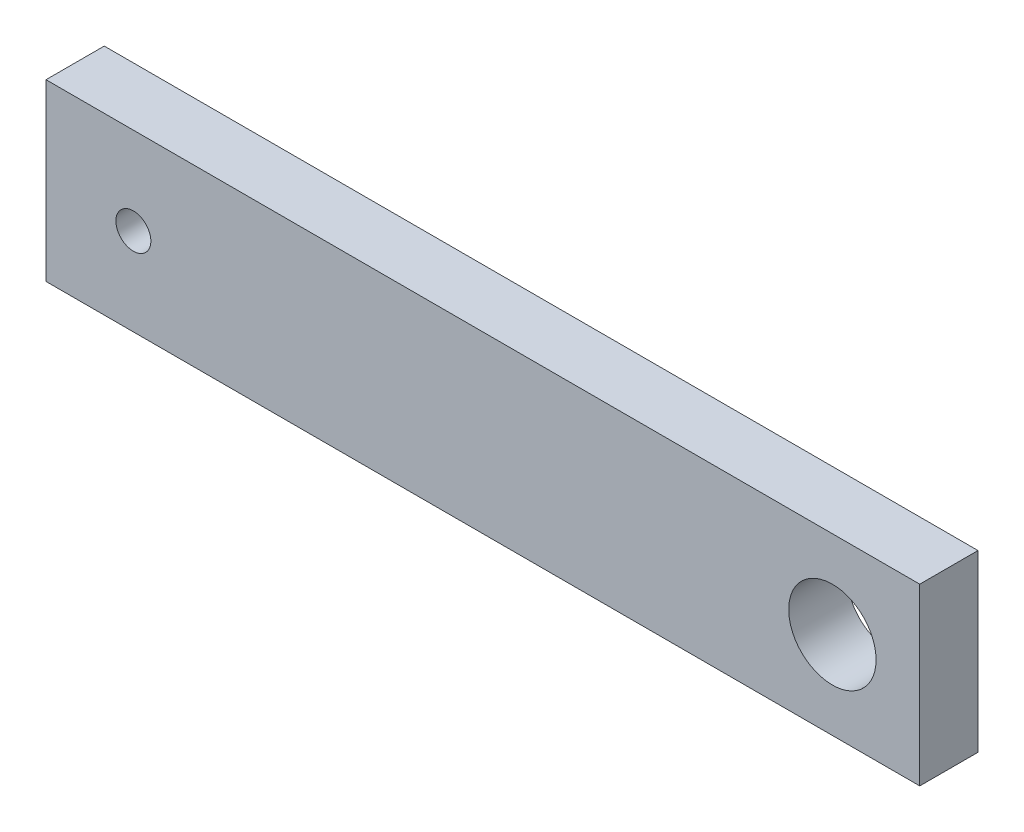
SolidWorks part; units mm, degrees
ref_plane "Front Plane" through (0, 0, 0) normal (0, 0, 1) x (1, 0, 0)
ref_plane "Top Plane" through (0, 0, 0) normal (0, 1, 0) x (1, 0, 0)
ref_plane "Right Plane" through (0, 0, 0) normal (1, 0, 0) x (0, 0, -1)
sketch "Sketch1" plane through (0, 0, 0) normal (0, 0, 1) x (1, 0, 0)
  line L1 (0, 0) -> (-30, 0)
  line L2 (0, 0) -> (0, 6)
  line L3 (0, 6) -> (-30, 6)
  line L4 (-30, 0) -> (-30, 6)
  circle A0 centre (-27, 3) radius 0.6
  circle A1 centre (-3, 3) radius 1.5
  dimension "D3" = 1.2
  dimension "D4" = 3
  dimension "D5" = 3
  dimension "D6" = 3
  dimension "D7" = 3
  dimension "D8" = 3
  dimension "D1" = 6
  dimension "D2" = 30
extrude "Boss-Extrude1" add sketch "Sketch1" along normal blind 2
